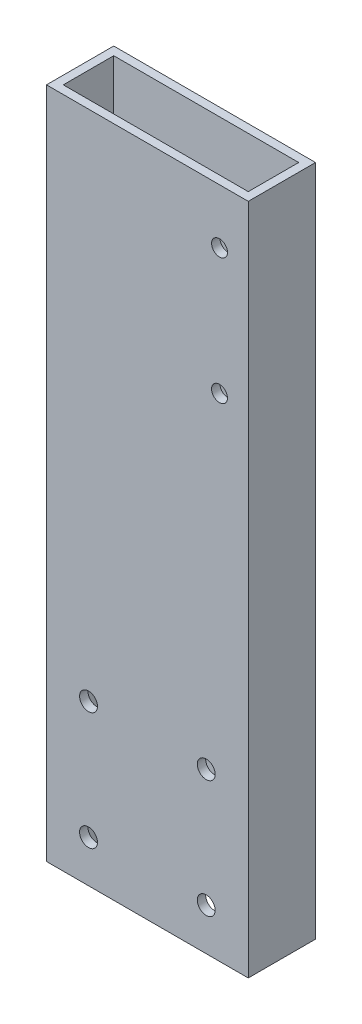
SolidWorks part; units mm, degrees
ref_plane "Front Plane" through (0, 0, 0) normal (0, 0, 1) x (1, 0, 0)
ref_plane "Top Plane" through (0, 0, 0) normal (0, 1, 0) x (1, 0, 0)
ref_plane "Right Plane" through (0, 0, 0) normal (1, 0, 0) x (0, 0, -1)
sketch "Sketch1" plane through (0, 0, 0) normal (0, 1, 0) x (1, 0, 0)
  line L0 (3.175, 3.175) -> (73.025, 3.175)
  line L1 (0, 0) -> (76.2, 0)
  line L2 (0, 0) -> (0, 25.4)
  line L3 (0, 25.4) -> (76.2, 25.4)
  line L4 (76.2, 0) -> (76.2, 25.4)
  line L5 (73.025, 3.175) -> (73.025, 22.225)
  line L6 (3.175, 22.225) -> (73.025, 22.225)
  line L7 (3.175, 3.175) -> (3.175, 22.225)
  dimension "D1" = 76.2
  dimension "D2" = 25.4
  dimension "D3" = 3.175
extrude "Boss-Extrude1" add sketch "Sketch1" along normal blind 254
sketch "Sketch2" plane through (0, 0, -25.4) normal (0, 0, -1) x (-1, 0, 0)
  line L0 (-15.875, 15.875) -> (-60.325, 15.875) construction
  line L1 (-60.325, 15.875) -> (-60.325, 60.325) construction
  line L2 (-60.325, 60.325) -> (-15.875, 60.325) construction
  line L3 (-15.875, 60.325) -> (-15.875, 15.875) construction
  line L4 (0, 254) -> (0, 0) construction
  line L5 (-76.2, 0) -> (0, 0) construction
  circle A0 centre (-60.325, 15.875) radius 3.3782
  circle A1 centre (-15.875, 15.875) radius 3.3782
  circle A2 centre (-15.875, 60.325) radius 3.3782
  circle A3 centre (-60.325, 60.325) radius 3.3782
  point P11 (-38.1, 15.875)
  point P12 (-60.325, 38.1)
  dimension "D1" = 6.7564
  dimension "D2" = 6.7564
  dimension "D3" = 6.7564
  dimension "D4" = 6.7564
  dimension "D5" = 44.45
  dimension "D6" = 38.1
  dimension "D7" = 38.1
  dimension "D9" = 44.45
extrude "Cut-Extrude1" cut sketch "Sketch2" against normal through all
sketch "Sketch3" plane through (0, 0, -25.4) normal (0, 0, -1) x (-1, 0, 0)
  circle A0 centre (-65.3474, 185.7375) radius 3
  circle A1 centre (-65.3474, 233.3625) radius 3
  dimension "D1" = 6
  dimension "D2" = 6
extrude "Cut-Extrude2" cut sketch "Sketch3" against normal through all
